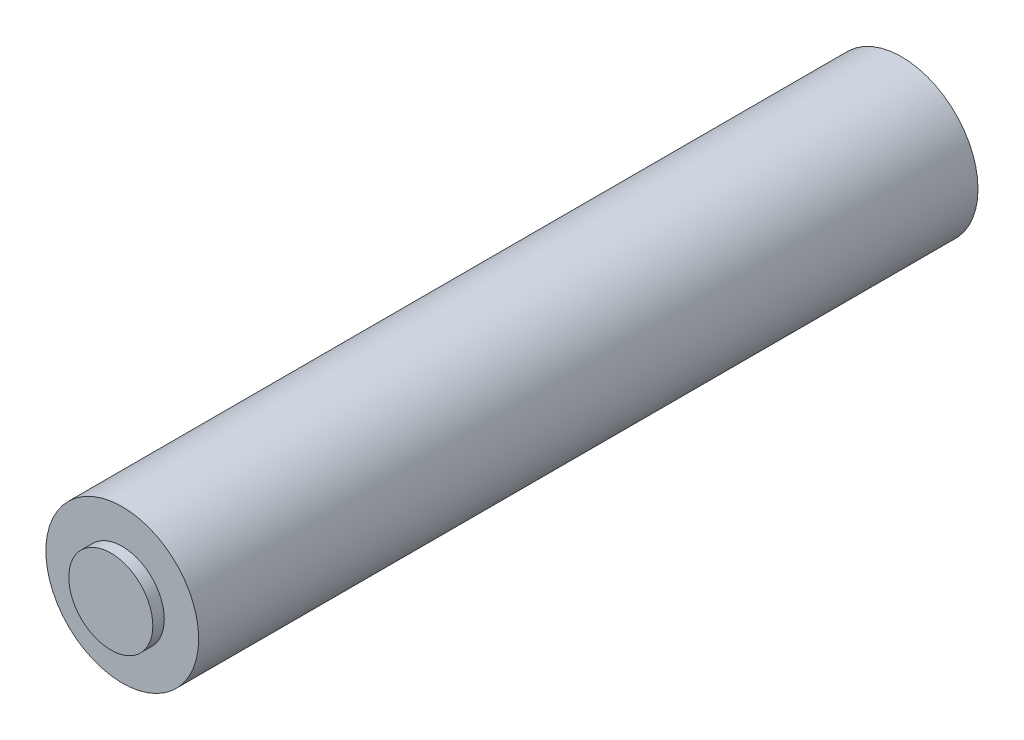
SolidWorks part; units mm, degrees
ref_plane "Alzado" through (0, 0, 0) normal (0, 0, 1) x (1, 0, 0)
ref_plane "Planta" through (0, 0, 0) normal (0, 1, 0) x (1, 0, 0)
ref_plane "Vista lateral" through (0, 0, 0) normal (1, 0, 0) x (0, 0, -1)
sketch "Croquis1" plane through (0, 0, 0) normal (0, 0, 1) x (1, 0, 0)
  circle A0 centre (0, 0) radius 10
  dimension "D1" = 20
extrude "Saliente-Extruir2" add sketch "Croquis1" along normal blind 102
sketch "Croquis2" plane through (0, 0, 102) normal (0, 0, 1) x (1, 0, 0)
  circle A0 centre (0, 0) radius 5.5
  dimension "D1" = 11
extrude "Saliente-Extruir3" add sketch "Croquis2" along normal blind 1.5 and the other way blind 103.5
